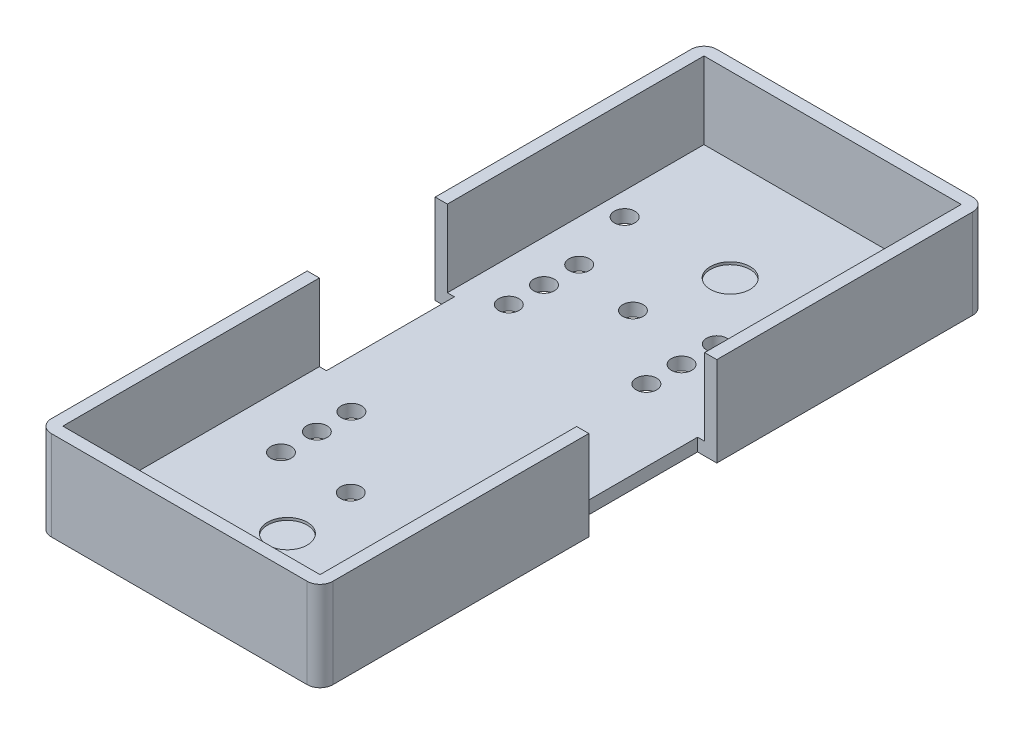
SolidWorks part; units mm, degrees
ref_plane "Front Plane" through (0, 0, 0) normal (0, 0, 1) x (1, 0, 0)
ref_plane "Top Plane" through (0, 0, 0) normal (0, 1, 0) x (1, 0, 0)
ref_plane "Right Plane" through (0, 0, 0) normal (1, 0, 0) x (0, 0, -1)
sketch "Sketch1" plane through (0, 0, 0) normal (0, 1, 0) x (1, 0, 0)
  line L1 (-11, -26) -> (11, -26)
  line L2 (-11, -26) -> (-11, 26)
  line L3 (-11, 26) -> (11, 26)
  line L4 (11, -26) -> (11, 26)
  line L5 (-11, -26) -> (11, 26) construction
  line L6 (-11, 26) -> (11, -26) construction
  point P0 (0, 0)
  dimension "D1" = 52
  dimension "D2" = 22
extrude "Boss-Extrude1" add sketch "Sketch1" along normal blind 7
sketch "Sketch2" plane through (0, 7, 0) normal (0, 1, 0) x (1, 0, 0)
  line L0 (-11, -26) -> (11, -26) construction
  line L1 (-10.05, -25.05) -> (10.05, -25.05)
  line L2 (-10.05, -25.05) -> (-10.05, 25.05)
  line L3 (-10.05, 25.05) -> (10.05, 25.05)
  line L4 (10.05, -25.05) -> (10.05, 25.05)
  line L5 (-10.05, -25.05) -> (10.05, 25.05) construction
  line L6 (-10.05, 25.05) -> (10.05, -25.05) construction
  line L8 (11, -26) -> (11, 26) construction
  point P0 (0, 0)
  dimension "D1" = 0.95
  dimension "D2" = 0.95
extrude "Cut-Extrude1" cut sketch "Sketch2" against normal blind 6
fillet "Fillet1" radius 1 4 edges at (-11, 3.5, 26) (11, 3.5, 26) (11, 3.5, -26) (-11, 3.5, -26)
sketch "Sketch3" plane through (0, 0, 0) normal (0, -1, 0) x (1, 0, 0)
  line L0 (0, -25) -> (0, 25) construction
  line L1 (-10, 0) -> (10, 0) construction
  line L2 (11, 25) -> (11, -25) construction
  line L3 (-11, -25) -> (-11, 25) construction
  line L4 (-10, 26) -> (10, 26) construction
  line L5 (10, -26) -> (-10, -26) construction
  line L6 (0, -23) -> (-10, -23) construction
  line L7 (-4.5, -25) -> (-7.5, -24) construction
  point P21 (-6, -24.5)
  dimension "D1" = 1
  dimension "D2" = 1
  dimension "D3" = 1
  dimension "D4" = 1
  dimension "D5" = 2
  dimension "D10" = 6
sketch "Sketch4" plane through (0, 0, 0) normal (0, -1, 0) x (1, 0, 0)
  line L0 (0, -25) -> (0, 25) construction
  line L1 (10, 0) -> (-10, 0) construction
  line L2 (11, 25) -> (11, -25) construction
  line L3 (-11, -25) -> (-11, 25) construction
  line L4 (10, -26) -> (-10, -26) construction
  line L5 (-10, 26) -> (10, 26) construction
  line L6 (-9.5, -5) -> (-9.5, 5)
  line L7 (-9.5, -5) -> (-11, -5)
  line L8 (-11, -5) -> (-11, 5)
  line L9 (-11, 5) -> (-9.5, 5)
  line L10 (11, -5) -> (11, 5)
  line L11 (11, 5) -> (9.5, 5)
  line L12 (9.5, -5) -> (9.5, 5)
  line L13 (9.5, -5) -> (11, -5)
  point P15 (-9.5, 0)
  dimension "D1" = 1
  dimension "D2" = 1
  dimension "D3" = 1
  dimension "D4" = 1
  dimension "D5" = 1.5
  dimension "D6" = 10
extrude "Cut-Extrude3" cut sketch "Sketch4" against normal through all
sketch "Sketch5" plane through (0, 1, 0) normal (0, 1, 0) x (1, 0, 0)
  line L0 (-9.5, 0) -> (9.5, 0) construction
  line L1 (-9.5, 5) -> (-9.5, -5) construction
  line L2 (9.5, -5) -> (9.5, 5) construction
  line L11 (-10.05, -25.05) -> (10.05, -25.05) construction
  circle A1 centre (0, -17.55) radius 1.55
  point P11 (0, 0)
  dimension "D2" = 7.5
extrude "Cut-Extrude4" cut sketch "Sketch5" against normal blind 0.2
sketch "Sketch6" plane through (0, 1, 0) normal (0, 1, 0) x (1, 0, 0)
  line L0 (0, 25) -> (0, -25) construction
  line L1 (10.05, 25.05) -> (-10.05, 25.05) construction
  circle A0 centre (0, 17.05) radius 1.55
  dimension "D2" = 3.1
  dimension "D1" = 8
extrude "Cut-Extrude5" cut sketch "Sketch6" against normal blind 0.2
sketch "Sketch7" plane through (0, 1, 0) normal (0, 1, 0) x (1, 0, 0)
  line L2 (-10.05, -5) -> (-10.05, -25.05) construction
  line L3 (-10.05, -25.05) -> (10.05, -25.05) construction
  circle A0 centre (-8.15, -23) radius 0.8
  dimension "D1" = 1.6
  dimension "D2" = 1.9
  dimension "D3" = 2.05
extrude "Cut-Extrude6" cut sketch "Sketch7" against normal through all both and the other way through all
sketch "Sketch8" plane through (0, 1, 0) normal (0, 1, 0) x (1, 0, 0)
  line L0 (-10.05, -5) -> (-10.05, -25.05) construction
  line L1 (-10.05, -25.05) -> (10.05, -25.05) construction
  circle A0 centre (-5.75, -12.3) radius 0.8
  circle A2 centre (5, -12.3) radius 0.8
  point P10 (3.5507, -12.3)
  dimension "D1" = 4.3
  dimension "D2" = 12.75
  dimension "D3" = 10.75
extrude "Cut-Extrude7" cut sketch "Sketch8" against normal up to next
sketch "Sketch9" plane through (0, 1, 0) normal (0, 1, 0) x (1, 0, 0)
  line L0 (-10.05, -5) -> (-10.05, -25.05) construction
  line L1 (-10.05, -25.05) -> (10.05, -25.05) construction
  circle A0 centre (-5.75, -9.5) radius 0.8
  circle A1 centre (5, -9.5) radius 0.8
  point P8 (5.0419, -9.5)
  dimension "D1" = 4.3
  dimension "D2" = 15.55
  dimension "D3" = 10.75
extrude "Cut-Extrude9" cut sketch "Sketch9" against normal up to next
sketch "Sketch10" plane through (0, 1, 0) normal (0, 1, 0) x (1, 0, 0)
  line L0 (-10.05, -5) -> (-10.05, -25.05) construction
  line L1 (-10.05, -25.05) -> (10.05, -25.05) construction
  circle A0 centre (-5.75, -6.8) radius 0.8
  circle A1 centre (5, -6.8372) radius 0.8
  dimension "D1" = 4.3
  dimension "D2" = 18.25
  dimension "D3" = 10.75
extrude "Cut-Extrude10" cut sketch "Sketch10" against normal up to next
sketch "Sketch11" plane through (0, 1, 0) normal (0, 1, 0) x (1, 0, 0)
  line L0 (-10.05, -25.05) -> (10.05, -25.05) construction
  line L1 (-10.05, -5) -> (-10.05, -25.05) construction
  circle A0 centre (-0.3, -12.3) radius 0.8
  dimension "D1" = 12.75
  dimension "D2" = 9.75
extrude "Cut-Extrude11" cut sketch "Sketch11" against normal up to next
sketch "Sketch12" plane through (0, 1, 0) normal (0, 1, 0) x (1, 0, 0)
  line L0 (10.05, 25.05) -> (-10.05, 25.05) construction
  line L1 (10.05, 5) -> (10.05, 25.05) construction
  circle A0 centre (3.95, 12.05) radius 0.8
  circle A1 centre (-6.8, 12.05) radius 0.8
  point P8 (-5.539, 12.05)
  dimension "D1" = 13
  dimension "D2" = 6.1
  dimension "D3" = 10.75
extrude "Cut-Extrude12" cut sketch "Sketch12" against normal up to next
sketch "Sketch13" plane through (0, 1, 0) normal (0, 1, 0) x (1, 0, 0)
  line L0 (10.05, 25.05) -> (-10.05, 25.05) construction
  line L1 (10.05, 5) -> (10.05, 25.05) construction
  circle A0 centre (3.95, 9.3) radius 0.8
  circle A1 centre (-6.8, 9.3) radius 0.8
  point P8 (-6.8173, 9.3)
  dimension "D1" = 15.75
  dimension "D2" = 6.1
  dimension "D3" = 10.75
extrude "Cut-Extrude13" cut sketch "Sketch13" against normal up to next
sketch "Sketch14" plane through (0, 1, 0) normal (0, 1, 0) x (1, 0, 0)
  line L0 (10.05, 25.05) -> (-10.05, 25.05) construction
  line L1 (10.05, 5) -> (10.05, 25.05) construction
  circle A0 centre (3.9, 6.6) radius 0.8
  circle A1 centre (-6.85, 6.6) radius 0.8
  point P8 (-6.7463, 6.6)
  dimension "D1" = 18.45
  dimension "D2" = 6.15
  dimension "D3" = 10.75
extrude "Cut-Extrude14" cut sketch "Sketch14" against normal up to next
sketch "Sketch15" plane through (0, 1, 0) normal (0, 1, 0) x (1, 0, 0)
  line L0 (10.05, 25.05) -> (-10.05, 25.05) construction
  line L1 (-10.05, 25.05) -> (-10.05, 5) construction
  circle A0 centre (-1.6, 11.05) radius 0.8
  dimension "D1" = 14
  dimension "D2" = 8.45
extrude "Cut-Extrude15" cut sketch "Sketch15" against normal up to next
sketch "Sketch16" plane through (0, 1, 0) normal (0, 1, 0) x (1, 0, 0)
  line L0 (10.05, 25.05) -> (-10.05, 25.05) construction
  line L1 (-10.05, 25.05) -> (-10.05, 5) construction
  circle A0 centre (-8.25, 17.05) radius 0.8
  dimension "D1" = 8
  dimension "D2" = 1.8
extrude "Cut-Extrude16" cut sketch "Sketch16" against normal up to next
